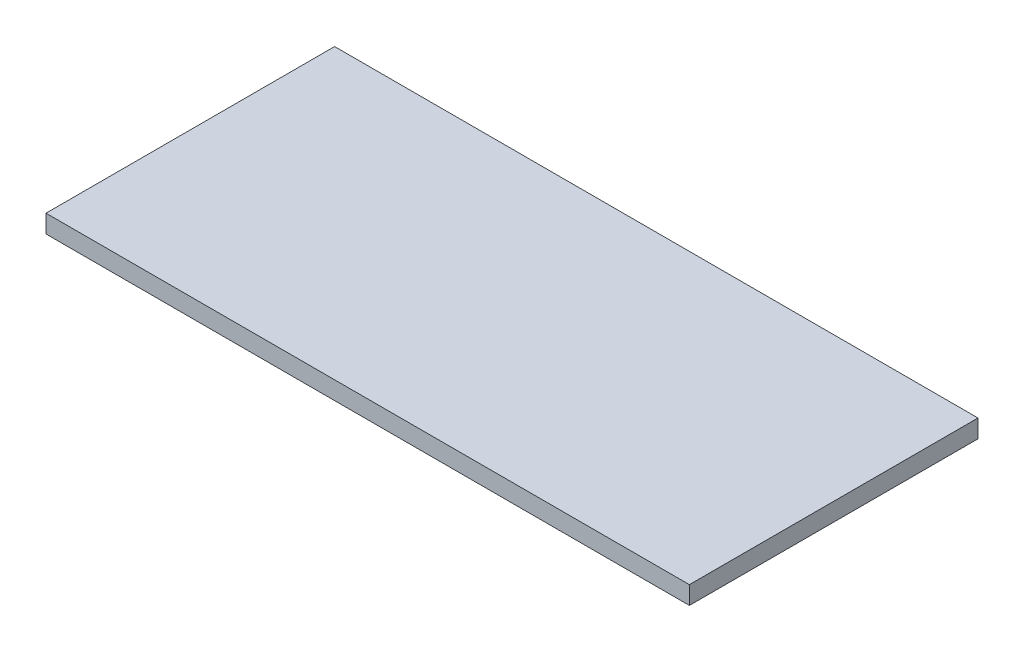
SolidWorks part; units mm, degrees
ref_plane "Front Plane" through (0, 0, 0) normal (0, 0, 1) x (1, 0, 0)
ref_plane "Top Plane" through (0, 0, 0) normal (0, 1, 0) x (1, 0, 0)
ref_plane "Right Plane" through (0, 0, 0) normal (1, 0, 0) x (0, 0, -1)
sketch "Sketch1" plane through (0, 0, 0) normal (0, 1, 0) x (1, 0, 0)
  line L1 (321, -144) -> (-321, -144)
  line L2 (321, -144) -> (321, 144)
  line L3 (321, 144) -> (-321, 144)
  line L4 (-321, -144) -> (-321, 144)
  line L5 (321, -144) -> (-321, 144) construction
  line L6 (321, 144) -> (-321, -144) construction
  point P0 (0, 0)
  dimension "D1" = 288
  dimension "D2" = 642
extrude "Boss-Extrude1" add sketch "Sketch1" along normal blind 18
equation "\"H_DSP\"=18"
equation "\"D1@Boss-Extrude1\"=\"H_DSP\""
